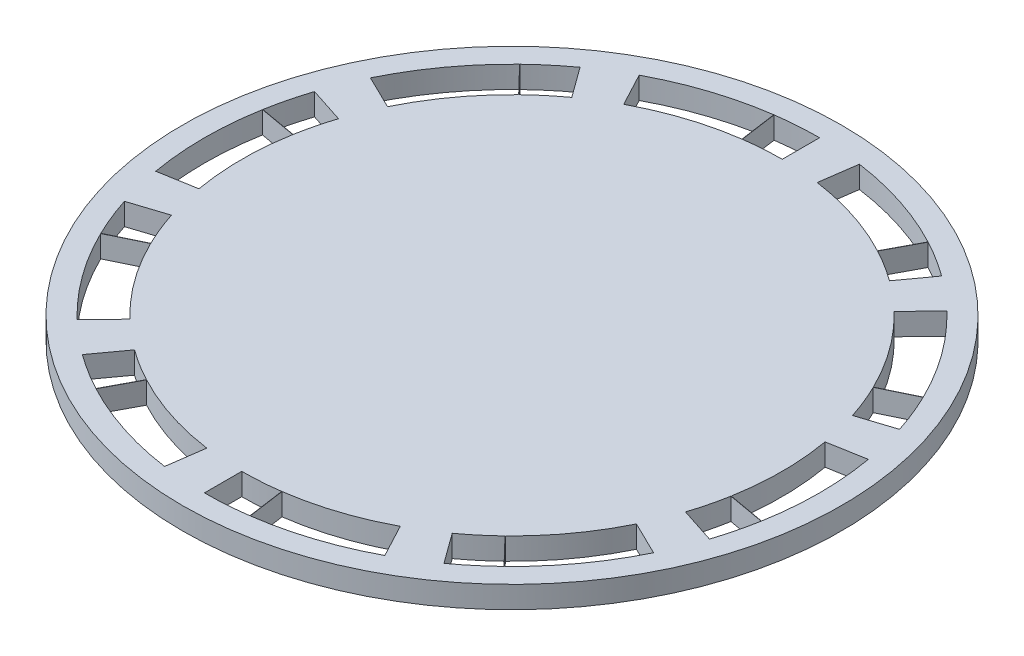
SolidWorks part; units mm, degrees
ref_plane "Front Plane" through (0, 0, 0) normal (0, 0, 1) x (1, 0, 0)
ref_plane "Top Plane" through (0, 0, 0) normal (0, 1, 0) x (1, 0, 0)
ref_plane "Right Plane" through (0, 0, 0) normal (1, 0, 0) x (0, 0, -1)
sketch "Sketch1" plane through (0, 0, 0) normal (0, 1, 0) x (1, 0, 0)
  line L0 (6.1244, 89.2817) -> (2.2434, 87.3888)
  line L1 (-1.1346, 99.273) -> (-4.1342, 96.1669)
  line L2 (-4.935, 102.4619) -> (-7.4731, 98.9685)
  line L3 (-9.1149, 105.0763) -> (-11.1454, 101.2655)
  line L4 (9.1831, 67.5183) -> (4.9307, 68.2681)
  line L5 (9.1831, 79.8682) -> (4.9307, 79.1184)
  line L6 (7.9829, 84.6819) -> (3.8762, 83.3475)
  line L7 (6.138, 89.2538) -> (2.2554, 87.3643)
  line L8 (-1.1346, 48.1135) -> (-4.1342, 51.2196)
  line L9 (6.1244, 58.1048) -> (2.2434, 59.9976)
  line L10 (7.9829, 62.7046) -> (3.8762, 64.0389)
  line L11 (9.1777, 67.4878) -> (4.9259, 68.2413)
  line L12 (-20.8877, 38.4793) -> (-21.4886, 42.7553)
  line L13 (-9.1423, 42.2956) -> (-11.1694, 46.1082)
  line L14 (-4.935, 44.9246) -> (-7.4731, 48.4179)
  line L15 (-1.157, 48.092) -> (-4.1538, 51.2007)
  line L16 (-42.5311, 42.2956) -> (-40.5039, 46.1082)
  line L17 (-30.7857, 38.4793) -> (-30.1847, 42.7553)
  line L18 (-25.8367, 38.1332) -> (-25.8367, 42.4512)
  line L19 (-20.9184, 38.475) -> (-21.5156, 42.7515)
  line L20 (-57.7978, 58.1048) -> (-53.9168, 59.9976)
  line L21 (-50.5387, 48.1135) -> (-47.5392, 51.2196)
  line L22 (-46.7383, 44.9246) -> (-44.2003, 48.4179)
  line L23 (-42.5585, 42.3102) -> (-40.528, 46.121)
  line L24 (-60.8564, 79.8682) -> (-56.604, 79.1184)
  line L25 (-60.8564, 67.5183) -> (-56.604, 68.2681)
  line L26 (-59.6562, 62.7046) -> (-55.5496, 64.0389)
  line L27 (-57.8114, 58.1327) -> (-53.9287, 60.0222)
  line L28 (-50.5387, 99.273) -> (-47.5392, 96.1669)
  line L29 (-57.7978, 89.2817) -> (-53.9168, 87.3888)
  line L30 (-59.6562, 84.6819) -> (-55.5496, 83.3475)
  line L31 (-60.851, 79.8987) -> (-56.5993, 79.1452)
  line L32 (-30.7857, 108.9072) -> (-30.1847, 104.6312)
  line L33 (-42.5311, 105.0909) -> (-40.5039, 101.2783)
  line L34 (-46.7383, 102.4619) -> (-44.2003, 98.9685)
  line L35 (-50.5164, 99.2945) -> (-47.5196, 96.1858)
  line L179 (-25.8367, 109.2532) -> (-25.8367, 104.9352)
  line L180 (-25.8367, 73.6932) -> (-20.8877, 108.9072) construction
  line L181 (-25.8367, 73.6932) -> (-30.7549, 108.9115) construction
  line L182 (-30.7549, 108.9115) -> (-30.1577, 104.635)
  line L183 (-20.8877, 108.9072) -> (-21.4886, 104.6312)
  line L186 (-9.1423, 105.0909) -> (-11.1694, 101.2783)
  arc A0 (-30.7549, 108.9115) -> (-25.8367, 109.2532) centre (-25.8367, 73.6932) cw
  circle A1 centre (-25.8367, 73.6932) radius 38.1
  arc A2 (-25.8367, 104.9352) -> (-30.1577, 104.635) centre (-25.8367, 73.6932) ccw
  arc A3 (-20.8877, 108.9072) -> (-9.1423, 105.0909) centre (-25.8367, 73.6932) cw
  arc A4 (-21.4886, 104.6312) -> (-11.1694, 101.2783) centre (-25.8367, 73.6932) cw
  arc A5 (-1.1346, 99.273) -> (6.1244, 89.2817) centre (-25.8367, 73.6932) cw
  arc A6 (-4.1342, 96.1669) -> (2.2434, 87.3888) centre (-25.8367, 73.6932) cw
  arc A7 (-9.1149, 105.0763) -> (-4.935, 102.4619) centre (-25.8367, 73.6932) cw
  arc A8 (-7.4731, 98.9685) -> (-11.1454, 101.2655) centre (-25.8367, 73.6932) ccw
  arc A9 (9.1831, 79.8682) -> (9.1831, 67.5183) centre (-25.8367, 73.6932) cw
  arc A10 (4.9307, 79.1184) -> (4.9307, 68.2681) centre (-25.8367, 73.6932) cw
  arc A11 (6.138, 89.2538) -> (7.9829, 84.6819) centre (-25.8367, 73.6932) cw
  arc A12 (3.8762, 83.3475) -> (2.2554, 87.3643) centre (-25.8367, 73.6932) ccw
  arc A13 (6.1244, 58.1048) -> (-1.1346, 48.1135) centre (-25.8367, 73.6932) cw
  arc A14 (2.2434, 59.9976) -> (-4.1342, 51.2196) centre (-25.8367, 73.6932) cw
  arc A15 (9.1777, 67.4878) -> (7.9829, 62.7046) centre (-25.8367, 73.6932) cw
  arc A16 (3.8762, 64.0389) -> (4.9259, 68.2413) centre (-25.8367, 73.6932) ccw
  arc A17 (-9.1423, 42.2956) -> (-20.8877, 38.4793) centre (-25.8367, 73.6932) cw
  arc A18 (-11.1694, 46.1082) -> (-21.4886, 42.7553) centre (-25.8367, 73.6932) cw
  arc A19 (-1.157, 48.092) -> (-4.935, 44.9246) centre (-25.8367, 73.6932) cw
  arc A20 (-7.4731, 48.4179) -> (-4.1538, 51.2007) centre (-25.8367, 73.6932) ccw
  arc A21 (-30.7857, 38.4793) -> (-42.5311, 42.2956) centre (-25.8367, 73.6932) cw
  arc A22 (-30.1847, 42.7553) -> (-40.5039, 46.1082) centre (-25.8367, 73.6932) cw
  arc A23 (-20.9184, 38.475) -> (-25.8367, 38.1332) centre (-25.8367, 73.6932) cw
  arc A24 (-25.8367, 42.4512) -> (-21.5156, 42.7515) centre (-25.8367, 73.6932) ccw
  arc A25 (-50.5387, 48.1135) -> (-57.7978, 58.1048) centre (-25.8367, 73.6932) cw
  arc A26 (-47.5392, 51.2196) -> (-53.9168, 59.9976) centre (-25.8367, 73.6932) cw
  arc A27 (-42.5585, 42.3102) -> (-46.7383, 44.9246) centre (-25.8367, 73.6932) cw
  arc A28 (-44.2003, 48.4179) -> (-40.528, 46.121) centre (-25.8367, 73.6932) ccw
  arc A29 (-60.8564, 67.5183) -> (-60.8564, 79.8682) centre (-25.8367, 73.6932) cw
  arc A30 (-56.604, 68.2681) -> (-56.604, 79.1184) centre (-25.8367, 73.6932) cw
  arc A31 (-57.8114, 58.1327) -> (-59.6562, 62.7046) centre (-25.8367, 73.6932) cw
  arc A32 (-55.5496, 64.0389) -> (-53.9287, 60.0222) centre (-25.8367, 73.6932) ccw
  arc A33 (-57.7978, 89.2817) -> (-50.5387, 99.273) centre (-25.8367, 73.6932) cw
  arc A34 (-53.9168, 87.3888) -> (-47.5392, 96.1669) centre (-25.8367, 73.6932) cw
  arc A35 (-60.851, 79.8987) -> (-59.6562, 84.6819) centre (-25.8367, 73.6932) cw
  arc A36 (-55.5496, 83.3475) -> (-56.5993, 79.1452) centre (-25.8367, 73.6932) ccw
  arc A37 (-42.5311, 105.0909) -> (-30.7857, 108.9072) centre (-25.8367, 73.6932) cw
  arc A38 (-40.5039, 101.2783) -> (-30.1847, 104.6312) centre (-25.8367, 73.6932) cw
  arc A39 (-50.5164, 99.2945) -> (-46.7383, 102.4619) centre (-25.8367, 73.6932) cw
  arc A40 (-44.2003, 98.9685) -> (-47.5196, 96.1858) centre (-25.8367, 73.6932) ccw
  point P80 (-25.8367, 73.6932)
  point P378 (-25.8367, 73.6932)
  dimension "D1" = 7.95
  dimension "D3" = 20
  dimension "D4" = 10
  dimension "D25" = 8
extrude "Boss-Extrude3" add sketch "Sketch1" along normal blind 2.54
